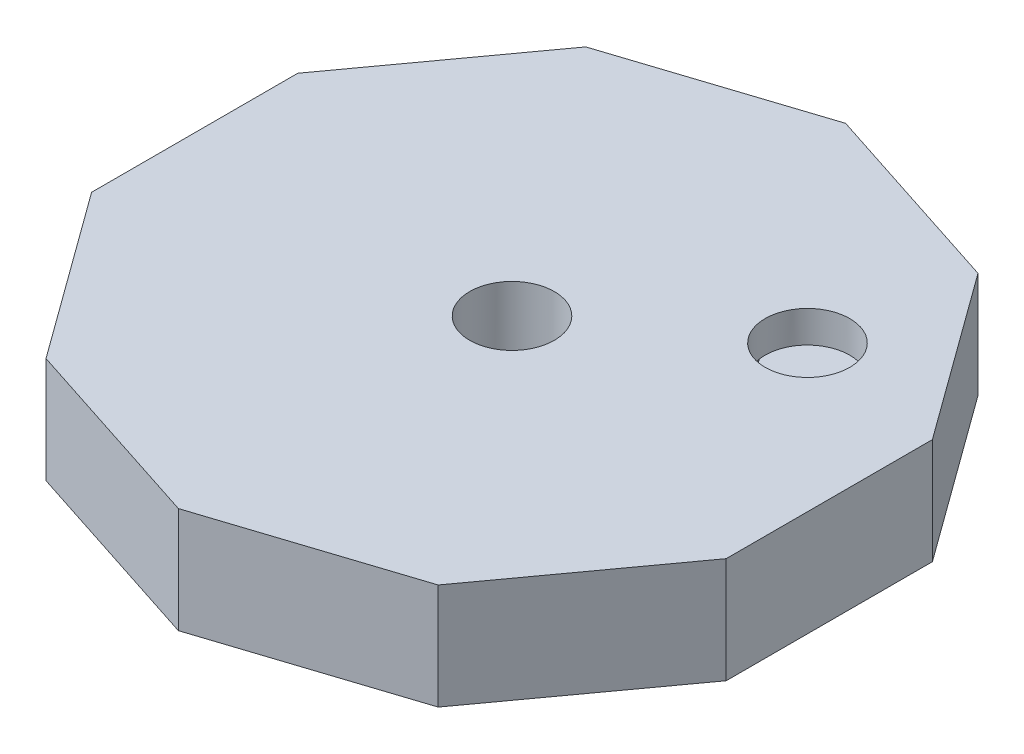
SolidWorks part; units mm, degrees
ref_plane "Front Plane" through (0, 0, 0) normal (0, 0, 1) x (1, 0, 0)
ref_plane "Top Plane" through (0, 0, 0) normal (0, 1, 0) x (1, 0, 0)
ref_plane "Right Plane" through (0, 0, 0) normal (1, 0, 0) x (0, 0, -1)
sketch "Sketch1" plane through (0, 0, 0) normal (0, 1, 0) x (1, 0, 0)
  line L0 (9.2705, -12.7598) -> (15, -4.8738)
  line L1 (0, 15.7719) -> (-9.2705, 12.7598)
  line L2 (-9.2705, 12.7598) -> (-15, 4.8738)
  line L3 (-15, 4.8738) -> (-15, -4.8738)
  line L4 (-15, -4.8738) -> (-9.2705, -12.7598)
  line L5 (-9.2705, -12.7598) -> (0, -15.7719)
  line L6 (0, -15.7719) -> (9.2705, -12.7598)
  line L7 (15, -4.8738) -> (15, 4.8738)
  line L8 (15, 4.8738) -> (9.2705, 12.7598)
  line L9 (9.2705, 12.7598) -> (0, 15.7719)
  circle A0 centre (0, 0) radius 15 construction
  dimension "D1" = 30
extrude "Boss-Extrude1" add sketch "Sketch1" along normal blind 5
sketch "Sketch2" plane through (0, 5, 0) normal (0, 1, 0) x (1, 0, 0)
  line L0 (12.1353, 8.8168) -> (0, 0) construction
  line L1 (15, 4.8738) -> (9.2705, 12.7598) construction
  circle A0 centre (0, 0) radius 2
  circle A1 centre (9.3037, 6.7595) radius 1.5
  dimension "D1" = 4
  dimension "D2" = 3
  dimension "D3" = 3.5
extrude "Cut-Extrude1" cut sketch "Sketch2" against normal blind 5 contours A0
sketch "Sketch4" plane through (0, 0, 0) normal (0, -1, 0) x (1, 0, 0)
  circle A0 centre (0, 0) radius 3
  dimension "D1" = 6
extrude "Cut-Extrude2" cut sketch "Sketch4" against normal blind 1.5
sketch "Sketch19" plane through (0, 0, 0) normal (0, -1, 0) x (1, 0, 0)
  line L1 (0, 0) -> (15, 0) construction
  line L3 (0, 0) -> (4.6353, -14.2658) construction
  line L4 (12.3607, 0) -> (3.8197, -11.7557) construction
  line L10 (0, -15.7719) -> (9.2705, -12.7598)
  line L11 (9.2705, -12.7598) -> (15, -4.8738)
  line L12 (15, -4.8738) -> (15, 4.8738)
  line L13 (15, 4.8738) -> (9.2705, 12.7598)
  line L14 (9.2705, 12.7598) -> (0, 15.7719)
  line L15 (0, 15.7719) -> (-9.2705, 12.7598)
  line L16 (-9.2705, 12.7598) -> (-15, 4.8738)
  line L17 (-15, 4.8738) -> (-15, -4.8738)
  line L18 (-15, -4.8738) -> (-9.2705, -12.7598)
  line L19 (-9.2705, -12.7598) -> (0, -15.7719)
  line L20 (0, -15.7719) -> (9.2705, -12.7598)
  line L21 (9.2705, -12.7598) -> (15, -4.8738)
  line L22 (15, -4.8738) -> (15, 4.8738)
  line L23 (15, 4.8738) -> (9.2705, 12.7598)
  line L24 (9.2705, 12.7598) -> (0, 15.7719)
  line L25 (0, 15.7719) -> (-9.2705, 12.7598)
  line L26 (-9.2705, 12.7598) -> (-15, 4.8738)
  line L27 (-15, 4.8738) -> (-15, -4.8738)
  line L28 (-15, -4.8738) -> (-9.2705, -12.7598)
  line L29 (-9.2705, -12.7598) -> (0, -15.7719)
  circle A1 centre (12.3607, 0) radius 2
  circle A3 centre (0, 0) radius 3 construction
  circle A4 centre (0, 0) radius 3
  circle A5 centre (3.8197, -11.7557) radius 2
  point P16 (-12.7219, 1.8326)
  point P23 (0, 0)
  dimension "D2" = 4
  dimension "D4" = 4
  dimension "D3" = 5
  dimension "D1" = 0
ref_plane "Plane4" through (8.0902, 0, -5.8779) normal (-0.809, 0, 0.5878) x (-0.5878, 0, -0.809)
sketch "Sketch23" plane through (8.0902, 0, -5.8779) normal (-0.809, 0, 0.5878) x (-0.5878, 0, -0.809)
  line L0 (9.2654, 0) -> (5.2654, 0) construction
  line L1 (-5.2654, 0) -> (-9.2654, 0) construction
  line L2 (9.2654, 0) -> (5.2654, 0)
  line L3 (-5.2654, 0) -> (-9.2654, 0)
  line L4 (-7.2654, 0) -> (-7.2654, -3)
  line L5 (7.2654, 0) -> (7.2654, -3)
  line L6 (-7.2654, -3) -> (7.2654, -3)
  dimension "D1" = 3
  dimension "D2" = 3
sketch "Sketch24" plane through (0, 0, 0) normal (0, -1, 0) x (1, 0, 0)
  circle A0 centre (3.8197, -11.7557) radius 2
  dimension "D1" = 4
sketch "Sketch25" plane through (0, 5, 0) normal (0, 1, 0) x (1, 0, 0)
  line L0 (3.8197, 11.7557) -> (12.3607, 0) construction
  line L10 (-9.2705, 12.7598) -> (-15, 4.8738)
  line L11 (-15, 4.8738) -> (-15, -4.8738)
  line L12 (-15, -4.8738) -> (-9.2705, -12.7598)
  line L13 (-9.2705, -12.7598) -> (0, -15.7719)
  line L14 (0, -15.7719) -> (9.2705, -12.7598)
  line L15 (9.2705, -12.7598) -> (15, -4.8738)
  line L16 (15, -4.8738) -> (15, 4.8738)
  line L17 (15, 4.8738) -> (9.2705, 12.7598)
  line L18 (9.2705, 12.7598) -> (0, 15.7719)
  line L19 (0, 15.7719) -> (-9.2705, 12.7598)
  line L20 (-9.2705, 12.7598) -> (-15, 4.8738)
  line L21 (-15, 4.8738) -> (-15, -4.8738)
  line L22 (-15, -4.8738) -> (-9.2705, -12.7598)
  line L23 (-9.2705, -12.7598) -> (0, -15.7719)
  line L24 (0, -15.7719) -> (9.2705, -12.7598)
  line L25 (9.2705, -12.7598) -> (15, -4.8738)
  line L26 (15, -4.8738) -> (15, 4.8738)
  line L27 (15, 4.8738) -> (9.2705, 12.7598)
  line L28 (9.2705, 12.7598) -> (0, 15.7719)
  line L29 (0, 15.7719) -> (-9.2705, 12.7598)
  circle A0 centre (8.0902, 5.8779) radius 2
  circle A1 centre (12.3607, 0) radius 2
  circle A2 centre (12.3607, 0) radius 2
  circle A3 centre (3.8197, 11.7557) radius 2
  circle A4 centre (3.8197, 11.7557) radius 2
  circle A5 centre (0, 0) radius 3
  circle A6 centre (0, 0) radius 3
  dimension "D5" = 4
  dimension "D6" = 5
  dimension "D1" = 0
  dimension "D2" = 0
  dimension "D3" = 0
  dimension "D4" = 0
extrude "Cut-Extrude3" cut sketch "Sketch25" against normal blind 2 contours A0
ref_plane "Plane5" through (8.0902, 0, -5.8779) normal (-0.809, 0, 0.5878) x (-0.5878, 0, -0.809)
extrude "Cut-Extrude4" cut sketch "Sketch19" against normal blind 3 contours A1 | A5
sketch "Sketch26" plane through (8.0902, 0, -5.8779) normal (-0.809, 0, 0.5878) x (-0.5878, 0, -0.809)
  line L0 (-7.2654, -3) -> (7.2654, -3) construction
  line L1 (-7.2654, -3) -> (7.2654, -3)
  line L3 (7.2654, -2.5) -> (-7.2654, -2.5)
  line L4 (7.2654, -2.5) -> (7.2654, -3.5)
  line L5 (7.2654, -3.5) -> (-7.2654, -3.5)
  line L6 (-7.2654, -2.5) -> (-7.2654, -3.5)
  line L7 (7.2654, -2.5) -> (-7.2654, -3.5) construction
  line L8 (7.2654, -3.5) -> (-7.2654, -2.5) construction
  point P2 (0, -3)
  dimension "D1" = 1
  dimension "D2" = 14.5309
extrude "Cut-Extrude5" cut sketch "Sketch26" against normal blind 2 and the other way blind 2 contours L3 L6 L5 L4
sketch "Sketch27" plane through (0, 0, 0) normal (0, -1, 0) x (1, 0, 0)
  circle A0 centre (0, 0) radius 3 construction
  circle A1 centre (0, 0) radius 3
  circle A2 centre (12.3607, 0) radius 2 construction
  circle A3 centre (12.3607, 0) radius 2
  circle A4 centre (3.8197, -11.7557) radius 2 construction
  circle A5 centre (3.8197, -11.7557) radius 2
  point P1 (0, 0)
  dimension "D1" = 14.5309
